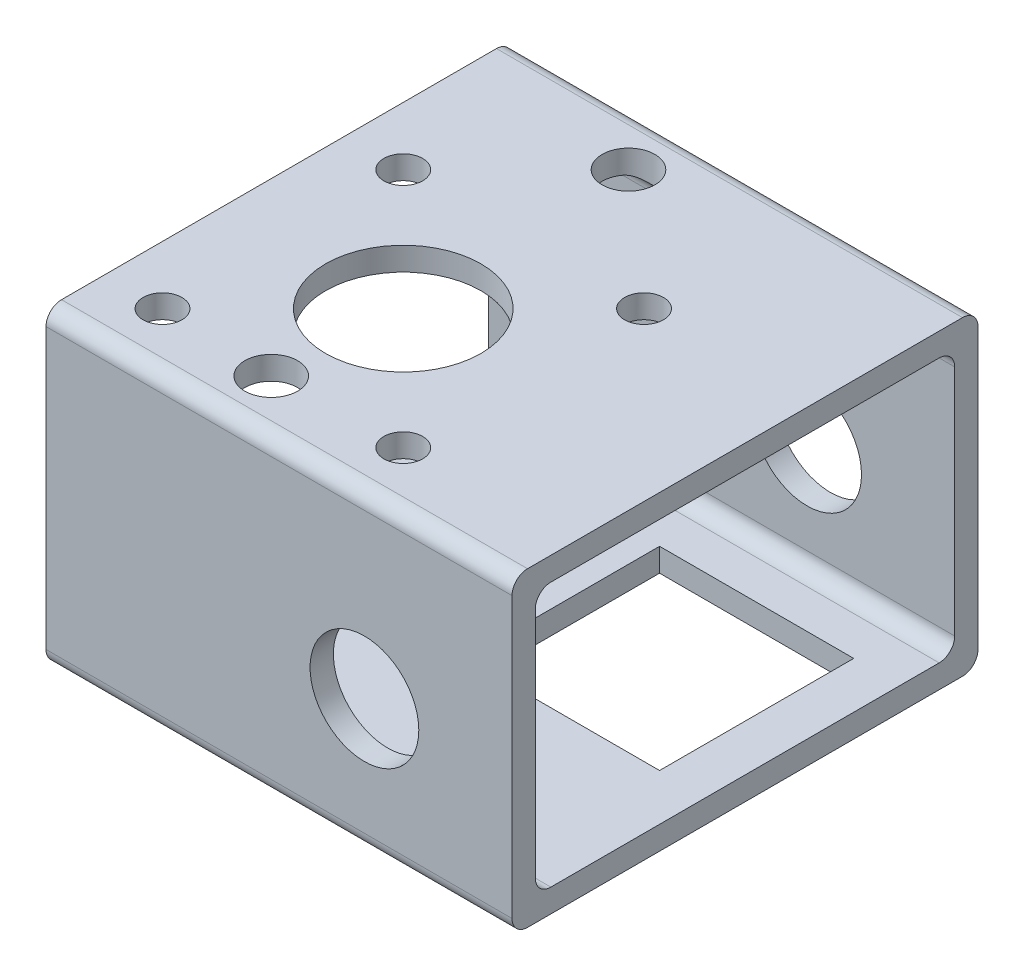
SolidWorks part; units mm, degrees
material "6061 合金"
ref_plane "前视基准面" through (0, 0, 0) normal (0, 0, 1) x (1, 0, 0)
ref_plane "上视基准面" through (0, 0, 0) normal (0, 1, 0) x (1, 0, 0)
ref_plane "右视基准面" through (0, 0, 0) normal (1, 0, 0) x (0, 0, -1)
sketch "草图1" plane through (0, 0, 0) normal (1, 0, 0) x (0, 0, -1)
  line L1 (3, 5) -> (3, 35)
  line L2 (5, 37) -> (55, 37)
  line L3 (57, 35) -> (57, 5)
  line L5 (60, 2) -> (60, 38)
  line L6 (58, 40) -> (2, 40)
  line L7 (0, 38) -> (0, 2)
  line L8 (58, 0) -> (2, 0)
  line L9 (55, 3) -> (5, 3)
  arc A0 (60, 38) -> (58, 40) centre (58, 38) ccw
  arc A1 (55, 37) -> (57, 35) centre (55, 35) cw
  arc A2 (3, 35) -> (5, 37) centre (5, 35) cw
  arc A3 (2, 40) -> (0, 38) centre (2, 38) ccw
  arc A4 (2, 0) -> (0, 2) centre (2, 2) cw
  arc A5 (5, 3) -> (3, 5) centre (5, 5) cw
  arc A6 (55, 3) -> (57, 5) centre (55, 5) ccw
  arc A7 (58, 0) -> (60, 2) centre (58, 2) ccw
  point P11 (60, 40)
  point P18 (0, 40)
  point P21 (0, 0)
  point P28 (60, 0)
  dimension "D6" = 2
  dimension "D8" = 2
  dimension "D1" = 3
  dimension "D2" = 3
  dimension "D3" = 3
  dimension "D4" = 60
  dimension "D5" = 40
  dimension "D7" = 3
extrude "凸台-拉伸1" add sketch "草图1" along normal blind 60
sketch "草图2" plane through (0, 40, 0) normal (0, 1, 0) x (1, 0, 0)
  line L0 (23, -19.2967) -> (23, 88.9945) construction
  line L1 (-21.8978, 23) -> (76.0197, 23) construction
  line L2 (60, 0) -> (0, 0) construction
  line L3 (0, 58) -> (0, 2) construction
  line L4 (-9.4226, 7.5) -> (65.353, 7.5) construction
  line L5 (7.5, -18.3438) -> (7.5, 73.6232) construction
  circle A0 centre (7.5, 7.5) radius 2.5
  circle A1 centre (38.5, 7.5) radius 2.5
  circle A2 centre (38.5, 38.5) radius 2.5
  circle A3 centre (7.5, 38.5) radius 2.5
  circle A4 centre (23, 23) radius 10
  dimension "D5" = 5
  dimension "D8" = 20
  dimension "D1" = 23
  dimension "D2" = 23
  dimension "D3" = 15.5
  dimension "D4" = 15.5
  dimension "D6" = 2
  dimension "D7" = 2
extrude "切除-拉伸1" cut sketch "草图2" against normal up to next
sketch "草图3" plane through (0, 0, 0) normal (0, 0, 1) x (1, 0, 0)
  line L0 (23, -15.1885) -> (23, 47.9229) construction
  line L1 (0, 38) -> (0, 2) construction
  line L2 (60, 40) -> (0, 40) construction
  circle A0 centre (41, 17) radius 7
  dimension "D1" = 14
  dimension "D2" = 23
  dimension "D3" = 18
  dimension "D4" = 23
extrude "切除-拉伸2" cut sketch "草图3" against normal through all
hole_wizard "M8 螺纹孔1" positions "草图4" profile "草图5" tap size "M8" standard "GB" end condition through all
sketch "草图4" plane through (0, 40, 0) normal (0, 1, 0) x (1, 0, 0)
  line L0 (60, 60) -> (0, 60) construction
  line L1 (0, 58) -> (0, 2) construction
  line L2 (60, 30) -> (0, 30) construction
  line L3 (60, 58) -> (60, 2) construction
  point P0 (22, 53)
  point P13 (22, 7)
  dimension "D1" = 7
  dimension "D2" = 22
cosmetic thread "孔螺蚊线1" parameters "D2"=8
cosmetic thread "孔螺蚊线2" parameters "D2"=8
sketch "草图5" plane through (22, 40, -53) normal (1, 0, 0) x (0, 0, 1)
  line L0 (0, 0) -> (0, 40)
  line L1 (0, 40) -> (3.4, 40)
  line L2 (3.4, 40) -> (3.4, 0)
  line L5 (3.4, 0) -> (0, 0)
  line L11 (0, -6.35) -> (0, 107.95) construction
  dimension "通孔螺纹孔钻头直径" = 6.8
  dimension "通孔螺纹孔钻头深度" = 40
sketch "草图6" plane through (0, 0, -60) normal (0, 0, -1) x (-1, 0, 0)
  line L0 (-18, 38) -> (-18, -10.7821) construction
  line L1 (-60, 38) -> (0, 38) construction
  line L3 (0, 2) -> (0, 38) construction
  line L4 (-18, 20) -> (0, 20) construction
  line L5 (0, 2) -> (0, 38) construction
  line L6 (-18, 20) -> (-1.0294, 3.0294) construction
  circle A1 centre (-9.5147, 11.5147) radius 2
  circle A2 centre (-26.4853, 11.5147) radius 2
  circle A3 centre (-26.4853, 28.4853) radius 2
  circle A4 centre (-9.5147, 28.4853) radius 2
  circle A5 centre (-18, 20) radius 12 construction
  point P6 (-13.4515, 11.4515)
  dimension "D2" = 4
  dimension "D1" = 24
  dimension "D3" = 45
  dimension "D4" = 18
extrude "切除-拉伸3" cut sketch "草图6" against normal up to next
sketch "草图7" plane through (0, 0, 0) normal (0, -1, 0) x (1, 0, 0)
  line L1 (29, -50) -> (54, -50)
  line L2 (29, -50) -> (29, -25)
  line L3 (29, -25) -> (54, -25)
  line L4 (54, -50) -> (54, -25)
  line L5 (60, -2) -> (60, -58) construction
  line L6 (60, -60) -> (0, -60) construction
  dimension "D1" = 25
  dimension "D2" = 25
  dimension "D3" = 6
  dimension "D4" = 10
extrude "切除-拉伸4" cut sketch "草图7" against normal up to next
